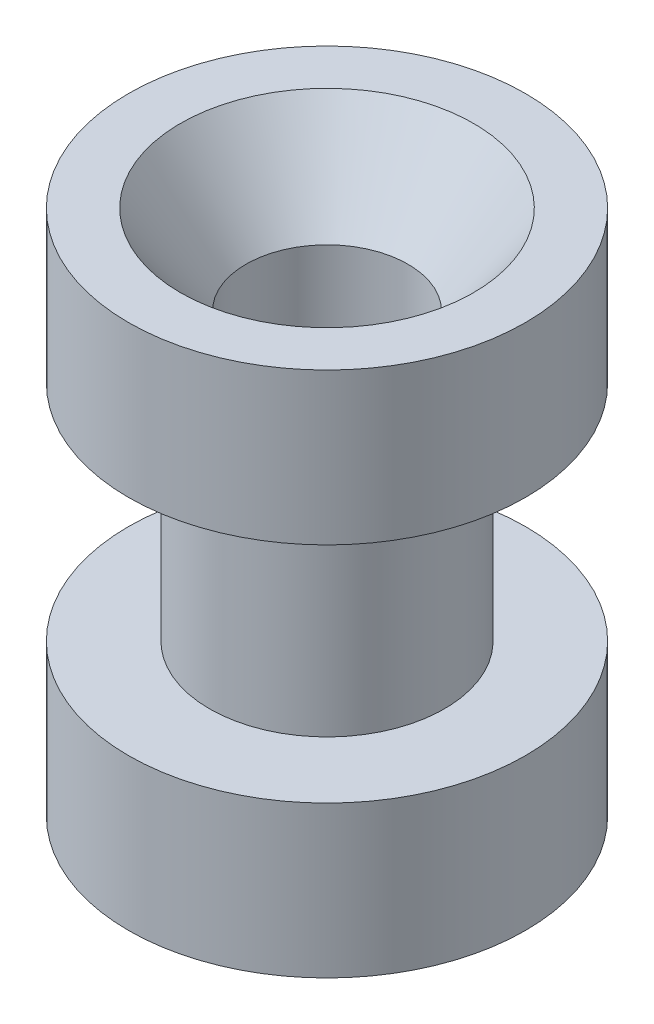
SolidWorks part; units mm, degrees
ref_plane "Front Plane" through (0, 0, 0) normal (0, 0, 1) x (1, 0, 0)
ref_plane "Top Plane" through (0, 0, 0) normal (0, 1, 0) x (1, 0, 0)
ref_plane "Right Plane" through (0, 0, 0) normal (1, 0, 0) x (0, 0, -1)
sketch "Sketch1" plane through (0, 0, 0) normal (0, 1, 0) x (1, 0, 0)
  circle A0 centre (0, 0) radius 6.223
  dimension "D2" = 12.446
extrude "Boss-Extrude1" add sketch "Sketch1" along normal blind 4.7498
sketch "Sketch2" plane through (0, 4.7498, 0) normal (0, 1, 0) x (1, 0, 0)
  circle A0 centre (0, 0) radius 3.683
  dimension "D1" = 7.366
extrude "Boss-Extrude2" add sketch "Sketch2" along normal blind 7.0104
sketch "Sketch3" plane through (0, 11.7602, 0) normal (0, 1, 0) x (1, 0, 0)
  circle A0 centre (0, 0) radius 6.223
  dimension "D1" = 12.446
extrude "Boss-Extrude3" add sketch "Sketch3" along normal blind 4.7498
sketch "Sketch4" plane through (0, 16.51, 0) normal (0, 1, 0) x (1, 0, 0)
  circle A0 centre (0, 0) radius 2.54
  dimension "D1" = 5.08
extrude "Cut-Extrude1" cut sketch "Sketch4" against normal up to surface (16.51 mm away) up to face at (0, 0, 6.223)
sketch "Sketch5" plane through (0, 0, 0) normal (1, 0, 0) x (0, 0, -1)
  line L0 (0, 16.51) -> (0, 13.716)
  line L1 (6.223, 16.51) -> (-6.223, 16.51) construction
  line L3 (4.5974, 16.51) -> (0, 16.51)
  line L4 (0, 13.716) -> (2.54, 13.716)
  line L5 (2.54, 13.716) -> (4.5974, 16.51)
  point P5 (1.8002, 13.716)
  dimension "D1" = 2.794
  dimension "D2" = 4.5974
  dimension "D3" = 2.54
revolve "Cut-Revolve1" cut sketch "Sketch5" angle 360 about L0
